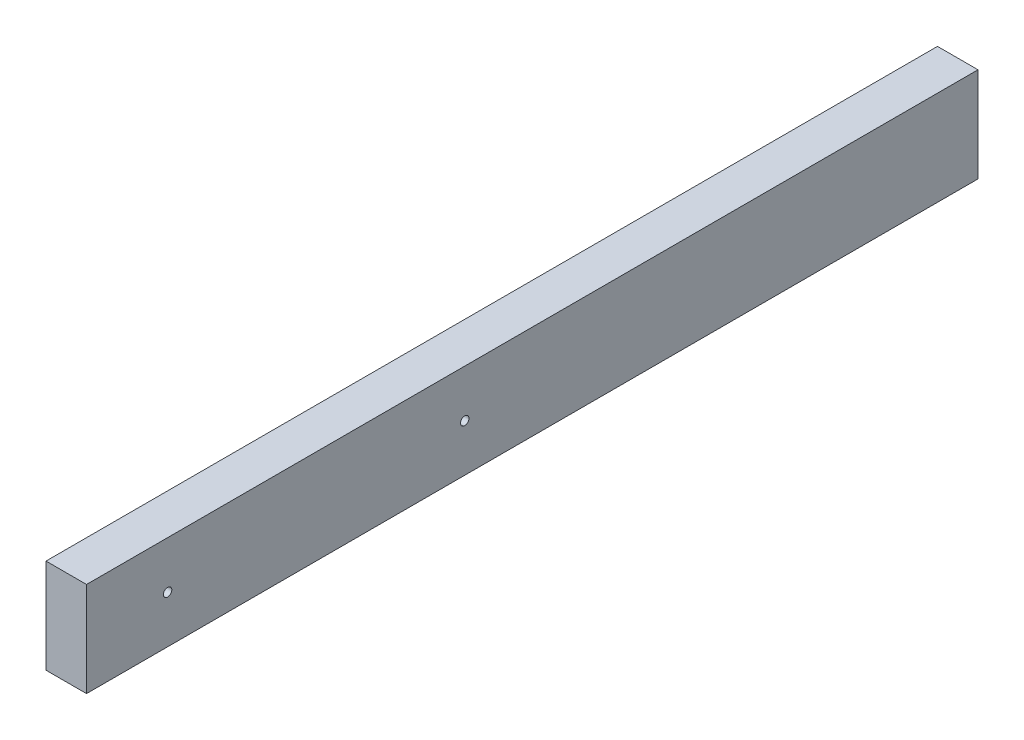
SolidWorks part; units mm, degrees
material "Pine"
ref_plane "Front Plane" through (0, 0, 0) normal (0, 0, 1) x (1, 0, 0)
ref_plane "Top Plane" through (0, 0, 0) normal (0, 1, 0) x (1, 0, 0)
ref_plane "Right Plane" through (0, 0, 0) normal (1, 0, 0) x (0, 0, -1)
sketch "Sketch1" plane through (0, 0, 0) normal (0, 0, 1) x (1, 0, 0)
  line L1 (-19.05, -44.45) -> (19.05, -44.45)
  line L2 (-19.05, -44.45) -> (-19.05, 44.45)
  line L3 (-19.05, 44.45) -> (19.05, 44.45)
  line L4 (19.05, -44.45) -> (19.05, 44.45)
  line L5 (-19.05, -44.45) -> (19.05, 44.45) construction
  line L6 (-19.05, 44.45) -> (19.05, -44.45) construction
  point P0 (0, 0)
  dimension "D1" = 88.9
  dimension "D2" = 38.1
extrude "Boss-Extrude1" add sketch "Sketch1" along normal blind 838.2
sketch "Sketch2" plane through (19.05, 0, 0) normal (1, 0, 0) x (0, 0, -1)
  line L1 (-838.2, -44.45) -> (-838.2, 44.45) construction
  point P0 (-482.6, 0)
  point P1 (-762, 0)
  dimension "D1" = 76.2
  dimension "D2" = 355.6
hole_wizard "5/16 (0.3125) Diameter Hole1" positions "Sketch4" profile "Sketch5" hole size "5/16" standard "ANSI Inch" end condition through all
sketch "Sketch4" plane through (19.05, 0, 0) normal (1, 0, 0) x (0, 0, -1)
  point P0 (-482.6, 0)
  point P3 (-762, 0)
sketch "Sketch5" plane through (19.05, 0, 482.6) normal (0, 1, 0) x (0, 0, -1)
  line L0 (0, 0) -> (0, 38.1)
  line L1 (0, 38.1) -> (3.9687, 38.1)
  line L2 (3.9687, 38.1) -> (3.9687, 0)
  line L5 (3.9687, 0) -> (0, 0)
  line L11 (0, -6.35) -> (0, 107.95) construction
  dimension "Thru Hole Dia." = 7.9375
  dimension "Thru Hole Depth" = 38.1
